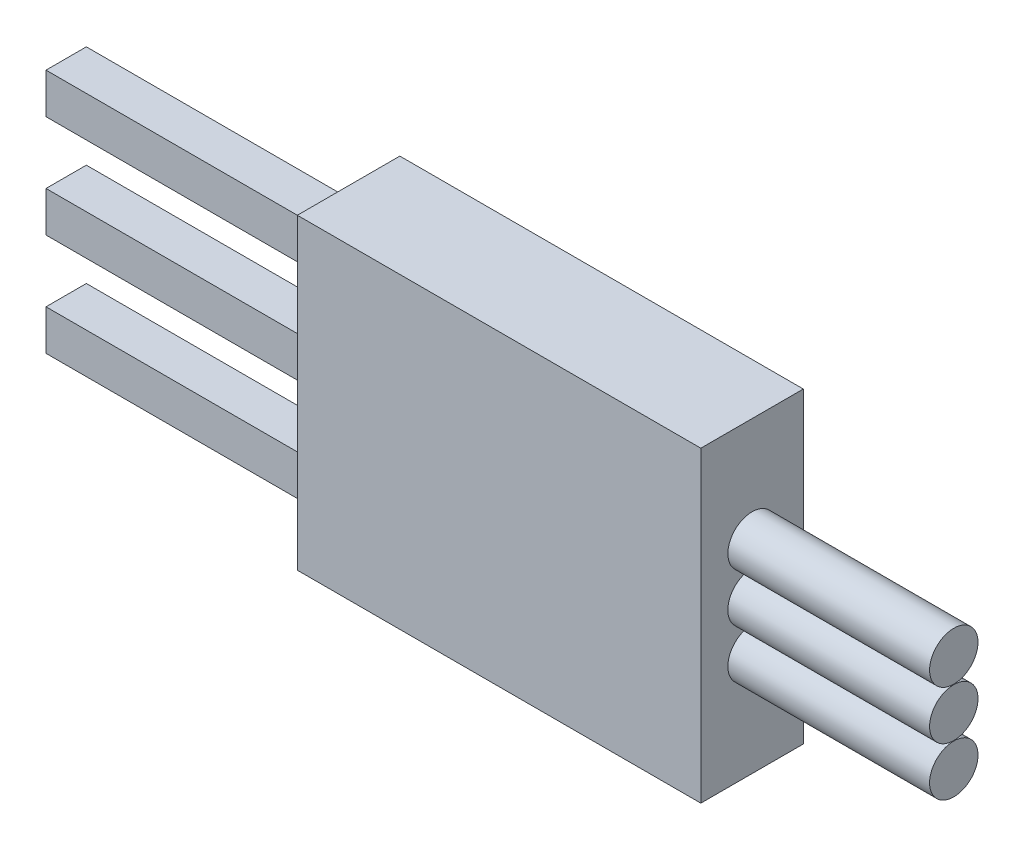
SolidWorks part; units mm, degrees
ref_plane "Alzado" through (0, 0, 0) normal (0, 0, 1) x (1, 0, 0)
ref_plane "Planta" through (0, 0, 0) normal (0, 1, 0) x (1, 0, 0)
ref_plane "Vista lateral" through (0, 0, 0) normal (1, 0, 0) x (0, 0, -1)
sketch "Croquis5" plane through (0, 0, 0) normal (0, 0, 1) x (1, 0, 0)
  line L0 (7.0112, -2.4331) -> (0.0112, -2.4331)
  line L1 (7.0112, -1.4331) -> (0.0112, -1.4331)
  line L2 (0.0112, -1.4331) -> (0.0112, -2.4331)
  line L3 (7.0112, -2.4331) -> (7.0112, -1.4331)
  line L4 (7.0112, 0.1069) -> (0.0112, 0.1069)
  line L5 (0.0112, 0.1069) -> (0.0112, 1.1069)
  line L6 (0.0112, 1.1069) -> (7.0112, 1.1069)
  line L7 (7.0112, 1.1069) -> (7.0112, 0.1069)
  line L8 (7.0112, 2.6469) -> (0.0112, 2.6469)
  line L9 (0.0112, 2.6469) -> (0.0112, 3.6469)
  line L10 (0.0112, 3.6469) -> (7.0112, 3.6469)
  line L11 (7.0112, 3.6469) -> (7.0112, 2.6469)
  line L12 (7.0112, -1.9331) -> (0.0112, -1.9331) construction
  line L13 (7.0112, 0.6069) -> (0.0112, 0.6069) construction
  line L14 (7.0112, 3.1469) -> (0.0112, 3.1469) construction
  dimension "D1" = 7
  dimension "D2" = 7
  dimension "D3" = 7
  dimension "D4" = 1
  dimension "D5" = 2.54
  dimension "D6" = 2.54
  dimension "D7" = 1
  dimension "D8" = 1
extrude "Saliente-Extruir1" add sketch "Croquis5" along normal blind 1
sketch "Croquis14" plane through (7.0112, 0, 0) normal (1, 0, 0) x (0, 0, -1)
  line L0 (0, 0.6069) -> (-1, 0.6069) construction
  line L1 (0, 0.1069) -> (0, 1.1069) construction
  line L2 (-1, 0.1069) -> (-1, 1.1069) construction
  line L3 (-0.5, 3.6469) -> (-0.5, -2.4331) construction
  line L4 (-1, 3.6469) -> (0, 3.6469) construction
  line L5 (-1, -2.4331) -> (0, -2.4331) construction
  line L6 (0.77, 4.4169) -> (-1.77, -3.2031) construction
  line L7 (0.77, 4.4169) -> (-1.77, 4.4169)
  line L8 (0.77, 4.4169) -> (0.77, -3.2031)
  line L9 (0.77, -3.2031) -> (-1.77, -3.2031)
  line L10 (-1.77, 4.4169) -> (-1.77, -3.2031)
  line L11 (0.77, -3.2031) -> (-1.77, 4.4169) construction
  dimension "D1" = 7.62
  dimension "D2" = 2.54
extrude "Saliente-Extruir2" add sketch "Croquis14" along normal blind 10
sketch "Croquis16" plane through (17.0112, 0, 0) normal (1, 0, 0) x (0, 0, -1)
  line L0 (0.77, 0.6069) -> (-1.77, 0.6069) construction
  line L1 (0.77, -3.2031) -> (0.77, 4.4169) construction
  line L2 (-1.77, 4.4169) -> (-1.77, -3.2031) construction
  line L3 (-0.5, 4.4169) -> (-0.5, -3.2031) construction
  line L4 (0.77, 4.4169) -> (-1.77, 4.4169) construction
  line L5 (-1.77, -3.2031) -> (0.77, -3.2031) construction
  circle A0 centre (-0.5, 0.6069) radius 0.6
  circle A1 centre (-0.5, 1.8169) radius 0.6
  circle A2 centre (-0.5, -0.6031) radius 0.6
extrude "Saliente-Extruir4" add sketch "Croquis16" along normal blind 5
